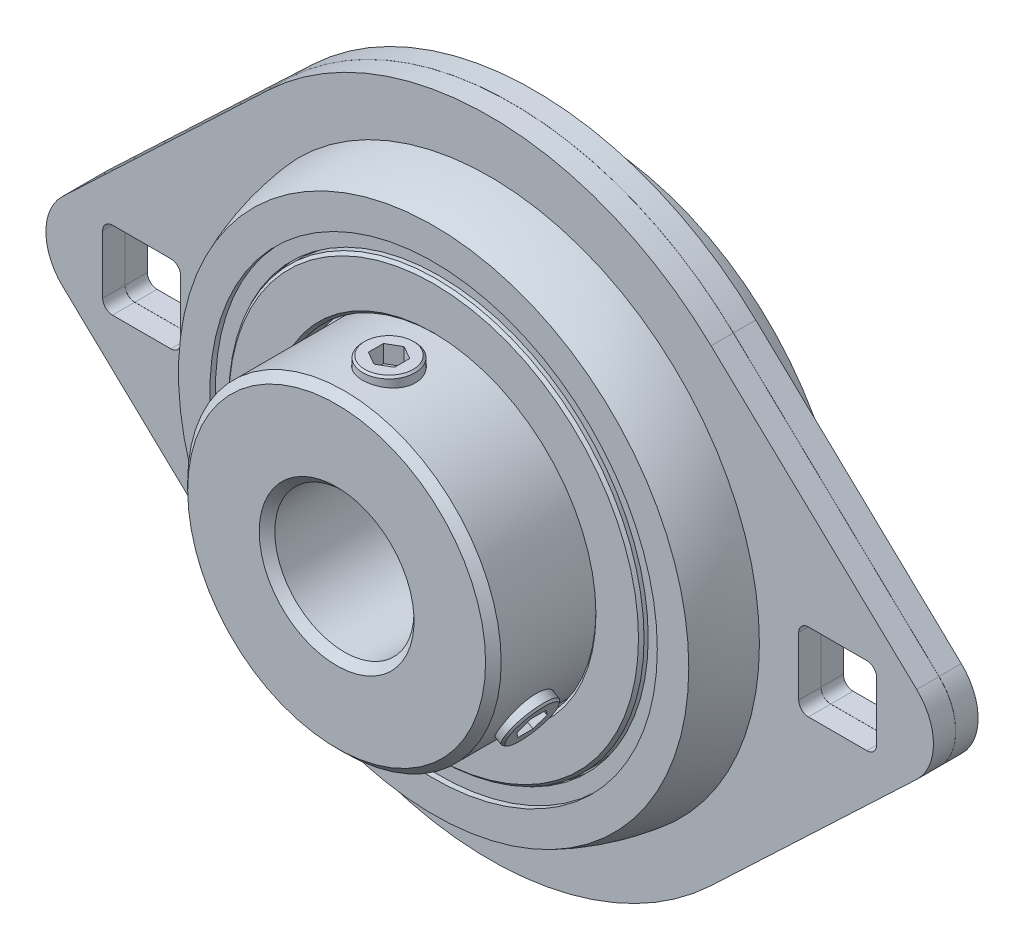
SolidWorks part; units mm, degrees
ref_plane "Front" through (0, 0, 0) normal (0, 0, 1) x (1, 0, 0)
ref_plane "Top" through (0, 0, 0) normal (0, 1, 0) x (1, 0, 0)
ref_plane "Right" through (0, 0, 0) normal (1, 0, 0) x (0, 0, -1)
sketch "Sketch1" plane through (0, 0, 0) normal (1, 0, 0) x (0, 0, -1)
  line L0 (-15.9995, 6.35) -> (5.9995, 6.35)
  line L1 (5.9995, 6.35) -> (5.9995, 14.3002)
  line L2 (5.9995, 14.3002) -> (2.6769, 14.3002)
  line L3 (-15.9995, 14.3002) -> (-15.9995, 6.35)
  line L4 (-4.8006, 19.3408) -> (4.8006, 19.3408) construction
  line L5 (4.8006, 19.3408) -> (4.8006, 21.6406) construction
  line L6 (-4.8006, 21.6374) -> (-4.8006, 19.3408) construction
  line L7 (0.0051, 29.3751) -> (0.0051, 22.6925)
  line L8 (5.1181, 21.872) -> (5.1181, 14.5542)
  line L10 (7.1501, 14.5542) -> (7.1501, 18.9449)
  line L11 (2.0371, 24.6118) -> (2.0371, 29.3751)
  line L12 (2.0371, 29.3751) -> (0.0051, 29.3751)
  line L13 (0.0051, 6.35) -> (1.8124, 22.5922) construction
  line L14 (1.8124, 22.5922) -> (2.0371, 24.6118) construction
  line L15 (0, 16.8205) -> (0, 29.3751) construction
  line L16 (0, 29.3751) -> (0.0051, 29.3751) construction
  line L17 (-2.0371, 29.3751) -> (-0.0051, 29.3751)
  line L18 (-2.0371, 24.6118) -> (-2.0371, 29.3751)
  line L19 (-7.1501, 14.5542) -> (-7.1501, 18.9449)
  line L21 (-5.1181, 21.872) -> (-5.1181, 14.5542)
  line L22 (-0.0051, 29.3751) -> (-0.0051, 22.6925)
  line L23 (-5.1181, 0) -> (5.1181, 0) construction
  line L24 (0, 0) -> (0, 6.35) construction
  line L25 (0.0051, 22.6925) -> (0.0051, 22.375) construction
  line L26 (4.8006, 21.6406) -> (5.1181, 21.6406) construction
  line L27 (0, 19.3408) -> (0, 20.421) construction
  line L28 (0, 14.3002) -> (0, 13.2201) construction
  line L29 (0, 20.421) -> (0, 20.4972) construction
  line L30 (-7.1501, 14.5542) -> (-5.1181, 14.5542)
  line L31 (-2.6769, 14.3002) -> (-15.9995, 14.3002)
  line L32 (5.1181, 14.5542) -> (7.1501, 14.5542)
  line L33 (2.6769, 14.3002) -> (-2.6769, 14.3002) construction
  line L34 (-7.1501, 18.9449) -> (-6.1341, 18.9449)
  line L35 (-6.1341, 18.9449) -> (-6.1341, 19.0719)
  line L36 (-6.1341, 19.0719) -> (-6.6421, 19.0719)
  line L37 (-6.6421, 19.0719) -> (-6.6421, 20.4085)
  line L38 (-6.6421, 20.4085) -> (-7.1501, 20.4085)
  line L39 (-7.1501, 20.4085) -> (-7.1501, 23.2784)
  line L40 (-6.1341, 18.9449) -> (-6.1341, 14.5542) construction
  line L41 (-6.6421, 19.0719) -> (-6.6421, 18.9449) construction
  line L42 (6.6421, 20.4085) -> (7.1501, 20.4085)
  line L43 (6.6421, 19.0719) -> (6.6421, 20.4085)
  line L44 (6.1341, 19.0719) -> (6.6421, 19.0719)
  line L45 (7.1501, 18.9449) -> (6.1341, 18.9449)
  line L46 (6.1341, 18.9449) -> (6.1341, 19.0719)
  line L47 (7.1501, 20.4085) -> (7.1501, 23.2784)
  arc A0 (4.8006, 21.6406) -> (-4.8006, 21.6374) centre (0.0051, 6.35) ccw construction
  arc A1 (0.0051, 22.6925) -> (5.1181, 21.872) centre (0.0051, 6.35) cw
  arc A2 (7.1501, 23.2784) -> (2.0371, 24.6118) centre (0.0051, 6.35) ccw
  circle A3 centre (0, 16.8205) radius 3.6004 construction
  arc A4 (-7.1501, 23.2784) -> (-2.0371, 24.6118) centre (-0.0051, 6.35) cw
  arc A5 (-0.0051, 22.6925) -> (-5.1181, 21.872) centre (-0.0051, 6.35) ccw
  arc A6 (-2.6769, 19.3408) -> (2.6769, 19.3408) centre (0, 16.8205) cw construction
  arc A7 (-2.6769, 14.3002) -> (2.6769, 14.3002) centre (0, 16.8205) ccw
  dimension "D4" = 7.2009
  dimension "Material Thickness t" = 2.032
  dimension "Shaft Dia" = 12.7
  dimension "Bearing Length Bi" = 21.9989
  dimension "Bearing Back n" = 5.9995
  dimension "Bearing Thickness M" = 7.145
  dimension "D1" = 0.0051
  dimension "OD b" = 58.7502
  dimension "D2" = 0.3175
  dimension "D3" = 9.6012
  dimension "D5" = 1.0801
  dimension "D6" = 0.0762
  dimension "D7" = 0.254
  dimension "Bearing OD K" = 28.6004
  dimension "D8" = 4.7633
  dimension "D9" = 0.127
  dimension "D10" = 7.3178
  dimension "D11" = 4.3907
  dimension "D12" = 1.4636
revolve "Revolve1" add sketch "Sketch1" angle 360 about L23
chamfer "Chamfer3" distance 0.254 angle 45 2 edges at (18.9449, 0, 7.1501) (14.5542, 0, 7.1501)
chamfer "Chamfer4" distance 0.254 angle 45 2 edges at (14.5542, 0, -7.1501) (18.9449, 0, -7.1501)
sketch "Sketch2" plane through (0, 0, 0) normal (1, 0, 0) x (0, 0, -1)
  line L0 (-4.8006, 19.3408) -> (4.8006, 19.3408) construction
  line L1 (4.8006, 19.3408) -> (4.8006, 21.6406) construction
  line L2 (-4.8006, 21.6374) -> (-4.8006, 19.3408) construction
  line L3 (-4.8006, 19.3408) -> (-2.6769, 19.3408)
  line L4 (4.8006, 19.3408) -> (4.8006, 21.6406)
  line L5 (-4.8006, 21.6374) -> (-4.8006, 19.3408)
  line L6 (2.6769, 19.3408) -> (4.8006, 19.3408)
  line L7 (-5.1181, 0) -> (5.1181, 0) construction
  line L8 (-5.1181, 0) -> (5.1181, 0) construction
  arc A0 (2.6769, 19.3408) -> (-2.6769, 19.3408) centre (0, 16.8205) ccw construction
  arc A1 (4.8006, 21.6406) -> (-4.8006, 21.6374) centre (0.0051, 6.35) ccw construction
  arc A2 (2.6769, 19.3408) -> (-2.6769, 19.3408) centre (0, 16.8205) ccw
  arc A3 (4.8006, 21.6406) -> (-4.8006, 21.6374) centre (0.0051, 6.35) ccw
revolve "Revolve2" add sketch "Sketch2" angle 360 about L8
sketch "Sketch3" plane through (0, 0, 0) normal (1, 0, 0) x (0, 0, -1)
  line L0 (0, 14.3002) -> (0, 13.2201) construction
  line L1 (0, 20.421) -> (0, 13.2201)
  circle A0 centre (0, 16.8205) radius 3.6004 construction
  arc A1 (0, 13.2201) -> (0, 20.421) centre (0, 16.8205) ccw
revolve "Revolve3" add sketch "Sketch3" angle 360 about L1
pattern_circular "CirPattern1" count 4 over 360 about axis through (0, 0, 0) along (0, 0, 1) of bodies 113
sketch "Sketch4" plane through (0, 0, 2.0371) normal (0, 0, 1) x (1, 0, 0)
  line L0 (-20.2029, 21.3246) -> (-38.9581, 3.556)
  line L1 (-38.9581, -3.556) -> (-20.2029, -21.3246)
  line L2 (-35.5891, 0) -> (35.5891, 0) construction
  line L3 (-31.75, -3.556) -> (-31.75, 3.556) construction
  line L4 (20.2029, -21.3246) -> (38.9581, -3.556)
  line L5 (38.9581, 3.556) -> (20.2029, 21.3246)
  line L6 (-35.306, -3.556) -> (-28.194, -3.556) construction
  line L7 (-35.306, -3.556) -> (-35.306, 3.556) construction
  line L8 (-35.306, 3.556) -> (-28.194, 3.556) construction
  line L9 (-28.194, -3.556) -> (-28.194, 3.556) construction
  line L10 (-20.2029, 21.3246) -> (20.2029, 21.3246) construction
  line L11 (0, 0) -> (0, 21.3246) construction
  line L12 (35.306, -3.556) -> (28.194, -3.556) construction
  line L13 (35.306, -3.556) -> (35.306, 3.556) construction
  line L14 (35.306, 3.556) -> (28.194, 3.556) construction
  line L15 (28.194, -3.556) -> (28.194, 3.556) construction
  line L16 (31.75, 3.556) -> (31.75, -3.556) construction
  arc A0 (-20.2029, 21.3246) -> (-20.2029, -21.3246) centre (0, 0) ccw
  arc A1 (-38.9581, 3.556) -> (-38.9581, -3.556) centre (-35.5891, 0) ccw
  arc A2 (38.9581, -3.556) -> (38.9581, 3.556) centre (35.5891, 0) ccw
  arc A3 (20.2029, -21.3246) -> (20.2029, 21.3246) centre (0, 0) ccw
  dimension "Overall Length a" = 80.9752
  dimension "Square length s" = 7.112
  dimension "Hole Distance e" = 63.5
extrude "Extrude1" add sketch "Sketch4" against normal up to surface (2.032 mm away) up to face at (29.3751, 0, 0.0051)
sketch "Sketch5" plane through (0, 0, -2.0371) normal (0, 0, -1) x (-1, 0, 0)
  line L0 (20.2029, 21.3246) -> (38.9581, 3.556) construction
  line L1 (38.9581, -3.556) -> (20.2029, -21.3246) construction
  line L2 (-20.2029, -21.3246) -> (-38.9581, -3.556) construction
  line L3 (-38.9581, 3.556) -> (-20.2029, 21.3246) construction
  line L4 (20.2029, 21.3246) -> (38.9581, 3.556)
  line L5 (38.9581, -3.556) -> (20.2029, -21.3246)
  line L6 (-20.2029, -21.3246) -> (-38.9581, -3.556)
  line L7 (-38.9581, 3.556) -> (-20.2029, 21.3246)
  arc A0 (38.9581, -3.556) -> (38.9581, 3.556) centre (35.5891, 0) ccw construction
  arc A1 (20.2029, -21.3246) -> (20.2029, 21.3246) centre (0, 0) ccw construction
  arc A2 (-38.9581, 3.556) -> (-38.9581, -3.556) centre (-35.5891, 0) ccw construction
  arc A3 (-20.2029, 21.3246) -> (-20.2029, -21.3246) centre (0, 0) ccw construction
  arc A4 (38.9581, -3.556) -> (38.9581, 3.556) centre (35.5891, 0) ccw
  arc A5 (20.2029, -21.3246) -> (20.2029, 21.3246) centre (0, 0) ccw
  arc A6 (-38.9581, 3.556) -> (-38.9581, -3.556) centre (-35.5891, 0) ccw
  arc A7 (-20.2029, 21.3246) -> (-20.2029, -21.3246) centre (0, 0) ccw
extrude "Extrude2" add sketch "Sketch5" against normal up to surface (2.032 mm away) up to face at (22.6925, 0, -0.0051)
sketch "Sketch6" plane through (0, 0, 0) normal (0, 0, 1) x (1, 0, 0)
  line L0 (35.306, -3.556) -> (28.194, -3.556) construction
  line L1 (35.306, -3.556) -> (35.306, 3.556) construction
  line L2 (35.306, 3.556) -> (28.194, 3.556) construction
  line L3 (28.194, -3.556) -> (28.194, 3.556) construction
  line L4 (-28.194, -3.556) -> (-28.194, 3.556) construction
  line L5 (-35.306, -3.556) -> (-28.194, -3.556) construction
  line L6 (-35.306, -3.556) -> (-35.306, 3.556) construction
  line L7 (-35.306, 3.556) -> (-28.194, 3.556) construction
  line L8 (35.306, -3.556) -> (28.194, -3.556)
  line L9 (35.306, -3.556) -> (35.306, 3.556)
  line L10 (35.306, 3.556) -> (28.194, 3.556)
  line L11 (28.194, -3.556) -> (28.194, 3.556)
  line L12 (-28.194, -3.556) -> (-28.194, 3.556)
  line L13 (-35.306, -3.556) -> (-28.194, -3.556)
  line L14 (-35.306, -3.556) -> (-35.306, 3.556)
  line L15 (-35.306, 3.556) -> (-28.194, 3.556)
extrude "Cut-Extrude1" cut sketch "Sketch6" against normal through all and the other way through all
fillet "Fillet1" radius 0.889 8 edges at (35.306, -3.556, -1.0211) (35.306, 3.556, -1.0211) (28.194, 3.556, -1.0211) (28.194, -3.556, -1.0211) (-35.306, -3.556, -1.0211) (-28.194, -3.556, -1.0211) (-28.194, 3.556, -1.0211) (-35.306, 3.556, -1.0211)
fillet "Fillet2" radius 0.889 8 edges at (35.306, -3.556, 1.0211) (28.194, -3.556, 1.0211) (28.194, 3.556, 1.0211) (35.306, 3.556, 1.0211) (-28.194, -3.556, 1.0211) (-28.194, 3.556, 1.0211) (-35.306, 3.556, 1.0211) (-35.306, -3.556, 1.0211)
chamfer "Chamfer1" distance 0.7112 angle 45 3 edges at (6.35, 0, -5.9995) (6.35, 0, 15.9995) (14.3002, 0, 15.9995)
sketch "Sketch7" plane through (0, 0, 0) normal (1, 0, 0) x (0, 0, -1)
  line L0 (-11.2192, 14.3002) -> (-11.2192, 6.35) construction
  line L1 (-2.6769, 14.3002) -> (-15.9995, 14.3002) construction
  line L2 (-15.9995, 6.35) -> (5.9995, 6.35) construction
  line L3 (-7.1501, 15.0622) -> (-7.1501, 14.3002) construction
  line L4 (-7.1501, 23.2784) -> (-7.1501, -23.2784) construction
  line L5 (-2.6769, 14.3002) -> (-15.2883, 14.3002) construction
  line L6 (-11.2192, 14.3002) -> (-13.6322, 14.3002) construction
  line L7 (-11.2192, 15.0622) -> (-15.2883, 15.0622) construction
  line L8 (-11.2192, 15.0622) -> (-7.1501, 15.0622) construction
  line L9 (-13.6322, 0) -> (-11.2192, 0)
  line L10 (-13.6322, 0) -> (-13.6322, 15.0622)
  line L11 (-13.6322, 15.0622) -> (-11.2192, 15.0622)
  line L12 (-11.2192, 0) -> (-11.2192, 15.0622)
  line L13 (0, 0) -> (-11.2192, 0) construction
  line L14 (-15.2883, 14.3002) -> (-15.2883, -14.3002) construction
  line L15 (-11.2192, 15.0622) -> (-11.2192, 16.8744) construction
  dimension "D1" = 0.762
  dimension "SD" = 4.826
revolve "Cut-Revolve2" cut sketch "Sketch7" angle 360 about L12
sketch "Sketch8" plane through (0, 0, 0) normal (1, 0, 0) x (0, 0, -1)
  line L0 (-13.6068, 15.0622) -> (-13.6068, 7.0979)
  line L1 (-13.6068, 7.0979) -> (-13.3346, 6.35)
  line L2 (-13.3346, 6.35) -> (-11.2192, 6.35)
  line L3 (-11.2192, 6.35) -> (-11.2192, 15.0622)
  line L4 (-13.6068, 15.0622) -> (-12.8109, 15.0622)
  line L6 (-11.2192, 0) -> (-11.2192, 15.0622) construction
  line L7 (-13.6322, 0) -> (-13.6322, 15.0622) construction
  line L8 (-15.9995, 6.35) -> (5.9995, 6.35) construction
  line L9 (-13.6322, 15.0622) -> (-11.2192, 15.0622) construction
  line L10 (-12.8109, 15.0622) -> (-12.015, 15.0622)
  line L11 (-12.015, 15.0622) -> (-11.2192, 15.0622)
  line L12 (-11.2192, 6.35) -> (-11.2192, -2.3622) construction
  line L14 (-8.8316, 15.0622) -> (-8.8316, 7.0979) construction
  dimension "D1" = 0.0254
  dimension "D2" = 70
  dimension "D3" = 4.7752
  dimension "D4" = 7.9643
revolve "Revolve4" add sketch "Sketch8" angle 360 about L3
chamfer "Chamfer2" distance 0.1778 angle 45 1 edges at (0, 15.0622, 8.8316)
sketch "Sketch9" plane through (0, 15.0622, 0) normal (0, 1, 0) x (-1, 0, 0)
  line L1 (0, 9.8407) -> (1.1938, 10.5299)
  line L2 (1.1938, 10.5299) -> (1.1938, 11.9084)
  line L3 (1.1938, 11.9084) -> (0, 12.5977)
  line L4 (0, 12.5977) -> (-1.1938, 11.9084)
  line L5 (-1.1938, 11.9084) -> (-1.1938, 10.5299)
  line L6 (-1.1938, 10.5299) -> (0, 9.8407)
  circle A0 centre (0, 11.2192) radius 1.1938 construction
  dimension "D1" = 2.3876
extrude "Cut-Extrude2" cut sketch "Sketch9" against normal blind 1.5929
pattern_circular "CirPattern2" count 2 every 120 of "Cut-Revolve2"
pattern_circular "CirPattern3" count 2 every 120 about axis through (0, 0, 0) along (0, 0, 1) of bodies 124
equation "\"D4@Sketch1\"=\"D3@Sketch1\"*.75"
equation "\"D5@Sketch1\"=\"D4@Sketch1\"*.15"
equation "\"D8@Sketch1\"=\"Bearing Thickness M@Sketch1\"*2/3"
equation "\"D1@Fillet1\"=\"Square length s@Sketch4\"/8"
equation "\"D1@Fillet2\"=\"D1@Fillet1\""
equation "\"D1@Chamfer1\"=\"Square length s@Sketch4\"/10"
equation "\"D1@Chamfer2\"=\"Square length s@Sketch4\"/40"
equation "\"D1@Sketch9\"=\"D3@Sketch8\"/2"
equation "\"D1@Cut-Extrude2\"=\"D4@Sketch8\"/5"
equation "\"D12@Sketch1\"=\"D10@Sketch1\"*.2"
equation "\"D11@Sketch1\"=\"D10@Sketch1\"*.6"
